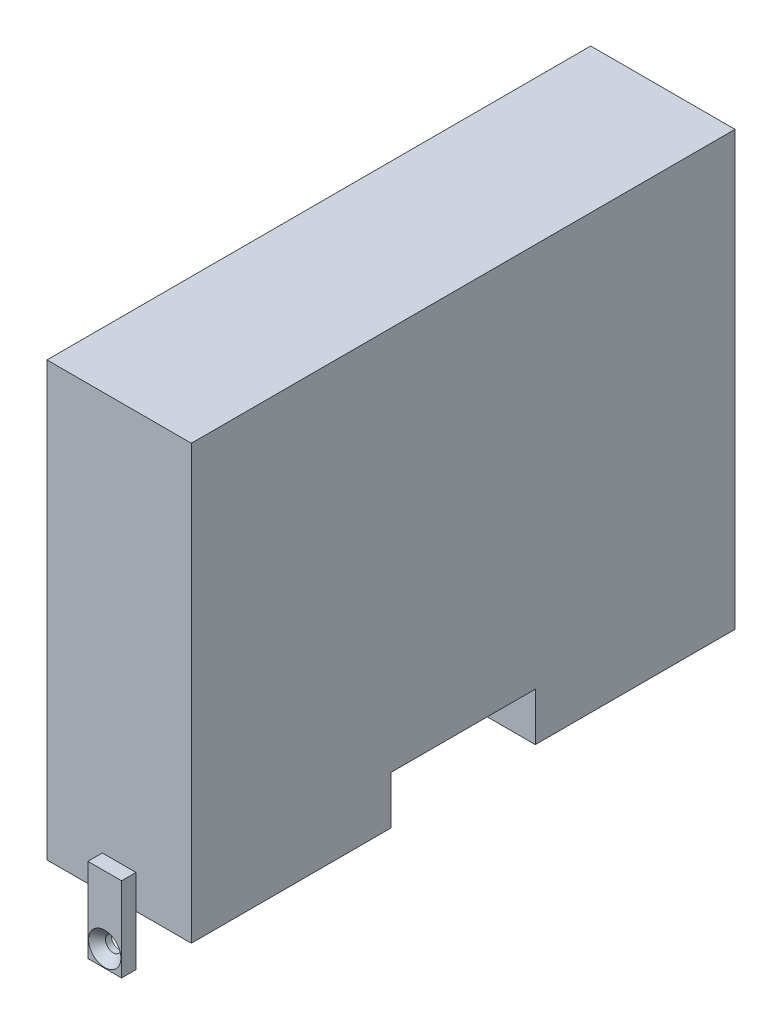
SolidWorks part; units mm, degrees
ref_plane "Front Plane" through (0, 0, 0) normal (0, 0, 1) x (1, 0, 0)
ref_plane "Top Plane" through (0, 0, 0) normal (0, 1, 0) x (1, 0, 0)
ref_plane "Right Plane" through (0, 0, 0) normal (1, 0, 0) x (0, 0, -1)
sketch "Sketch1" plane through (0, 0, 0) normal (0, 1, 0) x (1, 0, 0)
  line L1 (15, 56.5) -> (-15, 56.5)
  line L2 (15, 56.5) -> (15, -56.5)
  line L3 (15, -56.5) -> (-15, -56.5)
  line L4 (-15, 56.5) -> (-15, -56.5)
  line L5 (15, 56.5) -> (-15, -56.5) construction
  line L6 (15, -56.5) -> (-15, 56.5) construction
  point P0 (0, 0)
  dimension "D1" = 113
  dimension "D2" = 30
extrude "Boss-Extrude1" add sketch "Sketch1" along normal blind 90
sketch "Sketch3" plane through (0, 0, 0) normal (1, 0, 0) x (0, 0, -1)
  line L0 (-56.5, 90) -> (56.5, 90) construction
  line L1 (47.5, 85) -> (-47.5, 85)
  line L2 (47.5, 85) -> (47.5, 39.77)
  line L3 (47.5, 39.77) -> (-47.5, 39.77)
  line L4 (-47.5, 85) -> (-47.5, 39.77)
  point P4 (0, 39.77)
  dimension "D1" = 95
  dimension "D2" = 45.23
  dimension "D3" = 5
extrude "Cut-Extrude1" cut sketch "Sketch3" against normal blind 90 contours L4 L3 L2 L1
sketch "Sketch4" plane through (15, 0, 0) normal (1, 0, 0) x (0, 0, -1)
  line L0 (-56.5, 0) -> (56.5, 0) construction
  line L1 (-15, 0) -> (15, 0)
  line L2 (-15, 0) -> (-15, 10)
  line L3 (-15, 10) -> (15, 10)
  line L4 (15, 0) -> (15, 10)
  point P6 (0, 10)
  dimension "D1" = 30
  dimension "D2" = 10
extrude "Cut-Extrude2" cut sketch "Sketch4" against normal blind 10
sketch "Sketch6" plane through (0, 39.77, 0) normal (0, 1, 0) x (1, 0, 0)
  line L0 (15, 56.5) -> (-15, 56.5) construction
  line L1 (-15, 56.5) -> (-15, -56.5) construction
  line L3 (-15, -56.5) -> (15, -56.5) construction
  circle A0 centre (-8.5, 23.38) radius 2.5
  circle A2 centre (-8.5, -18.62) radius 2.5
  point P12 (-15, -22.6006)
  dimension "D1" = 5
  dimension "D4" = 5
  dimension "D2" = 33.12
  dimension "D3" = 6.5
  dimension "D5" = 37.88
  dimension "D6" = 6.5
hole_wizard "Ø5.0 (5) Diameter Hole1" positions "Sketch7" profile "Sketch8" hole size "Ø5.0" standard "ISO"
sketch "Sketch7" plane through (0, 39.77, 0) normal (0, 1, 0) x (1, 0, 0)
  point P0 (-8.5, 23.38)
  point P3 (-8.5, -18.62)
sketch "Sketch8" plane through (-8.5, 39.77, -23.38) normal (1, 0, 0) x (0, 0, 1)
  line L0 (0, 0) -> (0, 8)
  line L1 (0, 8) -> (2.5, 6.4978)
  line L2 (2.5, 6.4978) -> (2.5, 0.025)
  line L3 (2.5, 0.025) -> (2.525, 0)
  line L5 (2.525, 0) -> (0, 0)
  line L6 (-2.5, 0.025) -> (-2.525, 0) construction
  line L10 (0, 8) -> (-2.5, 6.4978) construction
  line L11 (0, -6.35) -> (0, 107.95) construction
  dimension "Hole Dia." = 5
  dimension "Hole Depth" = 8
  dimension "Near C'Sink Dia." = 5.05
  dimension "Near C'Sink Angle" = 90
  dimension "Drill Angle" = 118
sketch "Sketch9" plane through (0, 0, -56.5) normal (0, 0, -1) x (-1, 0, 0)
  line L5 (-15, 0) -> (15, 0) construction
  line L6 (3.5, 6.75) -> (-3.5, 6.75)
  line L7 (3.5, 6.75) -> (3.5, -10.75)
  line L8 (3.5, -10.75) -> (-3.5, -10.75)
  line L9 (-3.5, 6.75) -> (-3.5, -10.75)
  line L10 (3.5, 6.75) -> (-3.5, -10.75) construction
  line L11 (3.5, -10.75) -> (-3.5, 6.75) construction
  point P0 (0, -2)
  point P1 (0, 0)
  point P6 (0, -2.4086)
  dimension "D1" = 7
  dimension "D2" = 17.5
  dimension "D3" = 10.75
extrude "Boss-Extrude2" add sketch "Sketch9" along normal blind 3
sketch "Sketch11" plane through (0, 0, -59.5) normal (0, 0, -1) x (-1, 0, 0)
  line L0 (-3.5, -10.75) -> (3.5, -10.75) construction
  line L3 (3.5, -10.75) -> (3.5, 6.75) construction
  circle A0 centre (0, -7.25) radius 1.6
  dimension "D1" = 3.2
  dimension "D3" = 3.5
  dimension "D2" = 3.5
hole_wizard "CSK for M3 Hex Socket Countersunk Cap Screw1" positions "Sketch12" profile "Sketch13" countersink size "M3" standard "ISO"
sketch "Sketch12" plane through (0, 0, -59.5) normal (0, 0, -1) x (-1, 0, 0)
  point P0 (0, -7.25)
sketch "Sketch13" plane through (0, -7.25, -59.5) normal (1, 0, 0) x (0, 1, 0)
  line L0 (0, 0) -> (0, 8.2)
  line L1 (0, 8.2) -> (1.6, 7.2386)
  line L2 (1.6, 7.2386) -> (1.6, 1.76)
  line L3 (1.6, 1.76) -> (3.36, 0)
  line L5 (3.36, 0) -> (0, 0)
  line L6 (-1.6, 1.76) -> (-3.36, 0) construction
  line L10 (0, 8.2) -> (-1.6, 7.2386) construction
  line L11 (0, -6.35) -> (0, 107.95) construction
  dimension "Hole Dia." = 3.2
  dimension "Hole Depth" = 8.2
  dimension "Near C'Sink Dia." = 6.72
  dimension "Near C'Sink Angle" = 90
  dimension "Drill Angle" = 118
sketch "Sketch14" plane through (0, 0, 56.5) normal (0, 0, 1) x (1, 0, 0)
  line L0 (-15, 0) -> (15, 0) construction
  line L1 (3.5, 7) -> (-3.5, 7)
  line L2 (3.5, 7) -> (3.5, -10.5)
  line L3 (3.5, -10.5) -> (-3.5, -10.5)
  line L4 (-3.5, 7) -> (-3.5, -10.5)
  line L5 (3.5, 7) -> (-3.5, -10.5) construction
  line L6 (3.5, -10.5) -> (-3.5, 7) construction
  point P0 (0, 0)
  point P7 (0, 0)
  point P8 (0, 0)
  point P9 (0, 0)
  point P10 (0, 0)
  point P11 (0, 0)
  point P12 (0, 0)
  dimension "D1" = 17.5
  dimension "D2" = 10.5
extrude "Boss-Extrude3" add sketch "Sketch14" along normal blind 3
hole_wizard "CSK for M3 Hex Socket Countersunk Cap Screw2" positions "Sketch15" profile "Sketch16" countersink size "M3" standard "ISO"
sketch "Sketch15" plane through (0, 0, 59.5) normal (0, 0, 1) x (1, 0, 0)
  line L0 (3.5, -10.5) -> (3.5, 7) construction
  line L1 (-3.5, -10.5) -> (3.5, -10.5) construction
  point P0 (0, -7)
  dimension "D1" = 3.5
  dimension "D2" = 3.5
sketch "Sketch16" plane through (0, -7, 59.5) normal (1, 0, 0) x (0, -1, 0)
  line L0 (0, 0) -> (0, 8.2)
  line L1 (0, 8.2) -> (1.6, 7.2386)
  line L2 (1.6, 7.2386) -> (1.6, 1.76)
  line L3 (1.6, 1.76) -> (3.36, 0)
  line L5 (3.36, 0) -> (0, 0)
  line L6 (-1.6, 1.76) -> (-3.36, 0) construction
  line L10 (0, 8.2) -> (-1.6, 7.2386) construction
  line L11 (0, -6.35) -> (0, 107.95) construction
  dimension "Hole Dia." = 3.2
  dimension "Hole Depth" = 8.2
  dimension "Near C'Sink Dia." = 6.72
  dimension "Near C'Sink Angle" = 90
  dimension "Drill Angle" = 118
